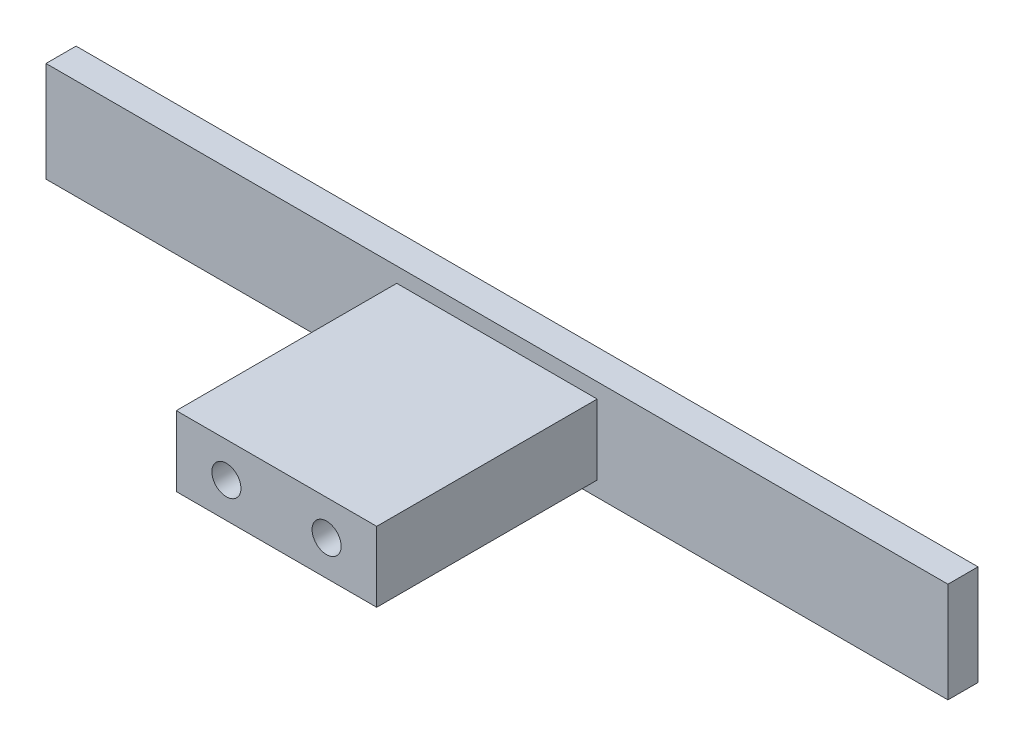
SolidWorks part; units mm, degrees
ref_plane "前视基准面" through (0, 0, 0) normal (0, 0, 1) x (1, 0, 0)
ref_plane "上视基准面" through (0, 0, 0) normal (0, 1, 0) x (1, 0, 0)
ref_plane "右视基准面" through (0, 0, 0) normal (1, 0, 0) x (0, 0, -1)
sketch "草图1" plane through (0, 0, 0) normal (0, 0, 1) x (1, 0, 0)
  line L1 (0, 0) -> (90, 0)
  line L2 (0, 0) -> (0, 10)
  line L3 (0, 10) -> (90, 10)
  line L4 (90, 0) -> (90, 10)
extrude "凸台-拉伸1" add sketch "草图1" along normal blind 3
sketch "草图2" plane through (0, 0, 3) normal (0, 0, 1) x (1, 0, 0)
  line L0 (0, 0) -> (0, 5)
  line L1 (0, 10) -> (0, 0) construction
  line L2 (0, 5) -> (90, 5)
  line L3 (90, 0) -> (90, 10) construction
  line L5 (35, 1.5) -> (55, 1.5)
  line L6 (35, 1.5) -> (35, 8.5)
  line L7 (35, 8.5) -> (55, 8.5)
  line L8 (55, 1.5) -> (55, 8.5)
  line L9 (35, 1.5) -> (55, 8.5) construction
  line L10 (35, 8.5) -> (55, 1.5) construction
  point P8 (45, 5)
extrude "凸台-拉伸3" add sketch "草图2" along normal blind 22 contours L5 L8 L7 L6
sketch "草图4" plane through (0, 0, 25) normal (0, 0, 1) x (1, 0, 0)
  line L0 (55, 8.5) -> (55, 1.5)
  line L1 (55, 1.5) -> (55, 5)
  line L2 (55, 5) -> (35, 5)
  line L3 (35, 1.5) -> (35, 8.5) construction
  line L4 (35, 5) -> (45, 5)
  line L5 (45, 5) -> (40, 5)
  line L6 (40, 5) -> (45, 5)
  line L7 (45, 5) -> (50, 5)
  circle A0 centre (50, 5) radius 1.45
  circle A1 centre (40, 5) radius 1.45
extrude "切除-拉伸1" cut sketch "草图4" against normal blind 9 contours L2 A0 | L2 A0 | L6 A1 L4 | L4 A1 L6
